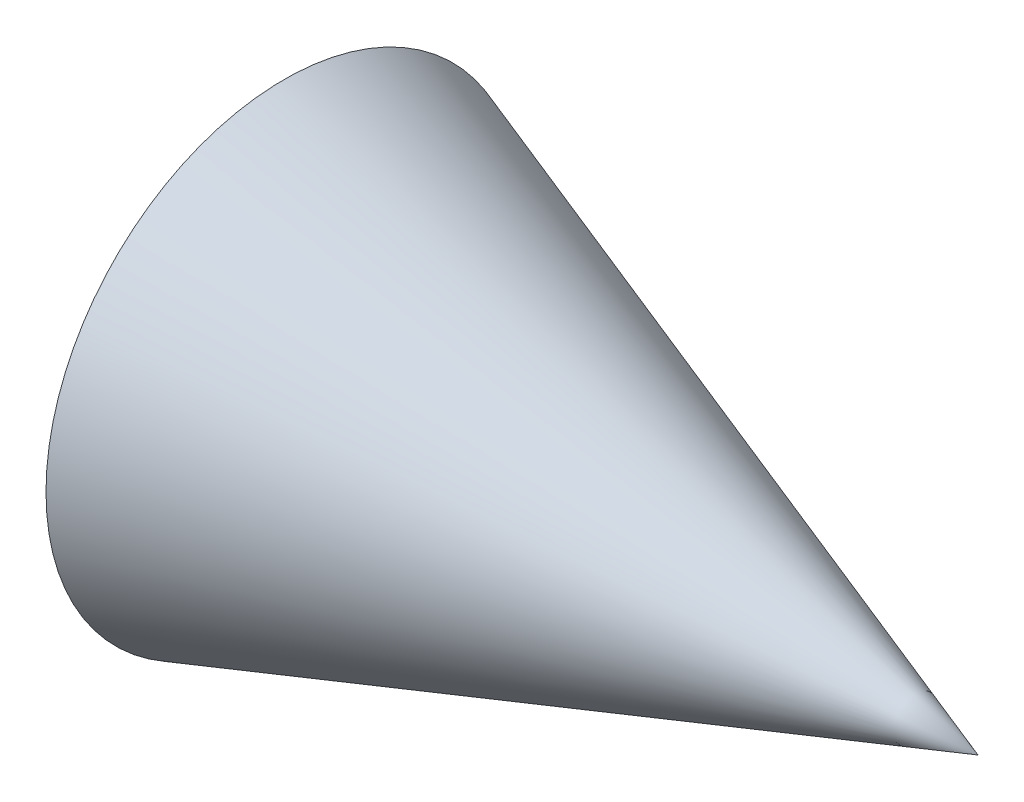
SolidWorks part; units mm, degrees
ref_plane "Front Plane" through (0, 0, 0) normal (0, 0, 1) x (1, 0, 0)
ref_plane "Top Plane" through (0, 0, 0) normal (0, 1, 0) x (1, 0, 0)
ref_plane "Right Plane" through (0, 0, 0) normal (1, 0, 0) x (0, 0, -1)
sketch "Sketch1" plane through (0, 0, 0) normal (0, 0, 1) x (1, 0, 0)
  line L0 (-35.7143, 0) -> (35.7143, 0) construction
  line L1 (0, 0) -> (0, 5.2)
  line L2 (0, 5.2) -> (15.1429, 0)
  line L3 (0, 0) -> (15.1429, 0)
  point P4 (0, 0)
  dimension "D1" = 5.2
sketch "Sketch2" plane through (0, 0, 0) normal (0, 0, 1) x (1, 0, 0)
revolve "Revolve1" add sketch "Sketch1" angle 360 about L0
